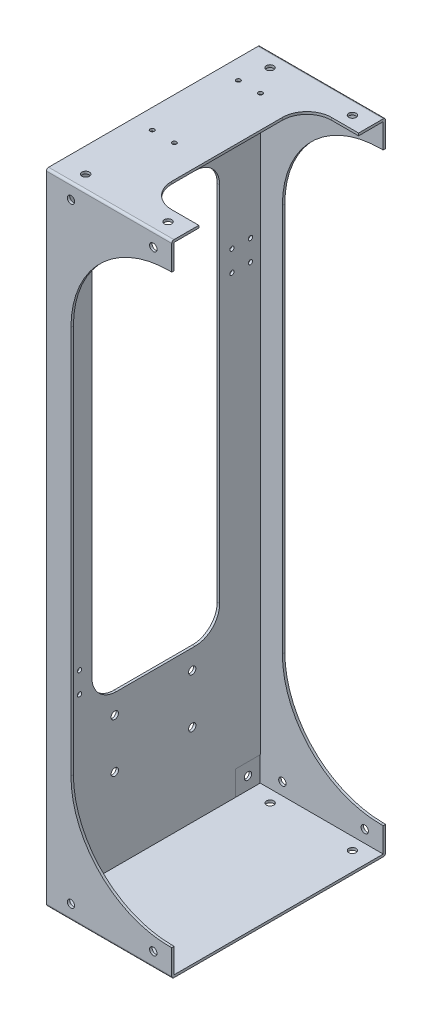
SolidWorks part; units mm, degrees
ref_plane "Front Plane" through (0, 0, 0) normal (0, 0, 1) x (1, 0, 0)
ref_plane "Top Plane" through (0, 0, 0) normal (0, 1, 0) x (1, 0, 0)
ref_plane "Right Plane" through (0, 0, 0) normal (1, 0, 0) x (0, 0, -1)
sketch "Sketch1" plane through (0, 0, 0) normal (1, 0, 0) x (0, 0, -1)
  line L0 (-87, 260) -> (87, -260) construction
  line L1 (-87, 260) -> (87, 260)
  line L2 (-87, 260) -> (-87, -260)
  line L3 (-87, -260) -> (87, -260)
  line L4 (87, 260) -> (87, -260)
  dimension "D1" = 520
  dimension "D2" = 174
extrude "Boss-Extrude1" add sketch "Sketch1" along normal blind 2
sketch "Sketch2" plane through (2, 0, 0) normal (1, 0, 0) x (0, 0, -1)
  line L8 (-85, 258) -> (-85, -258)
  line L9 (-85, -258) -> (85, -258)
  line L10 (85, -258) -> (85, 258)
  line L11 (85, 258) -> (-85, 258)
  line L12 (-85, 258) -> (-85, -258)
  line L13 (-85, -258) -> (85, -258)
  line L14 (85, -258) -> (85, 258)
  line L15 (85, 258) -> (-85, 258)
  line L16 (-87, 260) -> (-87, -260)
  line L17 (-87, -260) -> (87, -260)
  line L18 (87, -260) -> (87, 260)
  line L19 (87, 260) -> (-87, 260)
  line L20 (-87, 260) -> (-87, -260)
  line L21 (-87, -260) -> (87, -260)
  line L22 (87, -260) -> (87, 260)
  line L23 (87, 260) -> (-87, 260)
  dimension "D1" = 2
  dimension "D2" = 0
extrude "Boss-Extrude2" add sketch "Sketch2" along normal blind 100
sketch "Sketch3" plane through (0, 0, -87) normal (0, 0, 1) x (1, 0, 0)
  line L0 (102, 260) -> (0, 260) construction
  line L1 (102, 238) -> (100, 238)
  line L2 (20, 158) -> (20, -158)
  line L3 (100, -238) -> (102, -238)
  line L4 (0, 260) -> (0, -260) construction
  line L5 (102, 260) -> (102, -260) construction
  line L6 (102, -260) -> (0, -260) construction
  line L7 (102, 238) -> (102, -238)
  arc A0 (20, -158) -> (100, -238) centre (100, -158) ccw
  arc A1 (100, 238) -> (20, 158) centre (100, 158) ccw
  dimension "D3" = 80
  dimension "D2" = 20
  dimension "D11" = 22
  dimension "D12" = 22
extrude "Cut-Extrude1" cut sketch "Sketch3" along normal blind 10
sketch "Sketch4" plane through (0, 0, 87) normal (0, 0, 1) x (1, 0, 0)
  line L0 (102, 260) -> (0, 260) construction
  line L1 (102, 260) -> (102, -260) construction
  line L2 (102, -260) -> (0, -260) construction
  line L3 (0, 260) -> (0, -260) construction
  circle A0 centre (20, 248) radius 3
  circle A1 centre (87, 248) radius 3
  circle A2 centre (20, -248) radius 3
  circle A3 centre (87, -248) radius 3
  dimension "D2" = 6
  dimension "D1" = 12
  dimension "D3" = 15
  dimension "D4" = 12
  dimension "D5" = 20
extrude "Cut-Extrude2" cut sketch "Sketch4" against normal through all
sketch "Sketch5" plane through (0, 260, 0) normal (0, 1, 0) x (1, 0, 0)
  line L0 (20, 87) -> (20, 85) construction
  line L1 (87, 87) -> (87, 85) construction
  line L2 (102, -87) -> (0, -87) construction
  line L3 (102, 87) -> (0, 87) construction
  circle A0 centre (87, 75) radius 3
  circle A1 centre (20, 75) radius 3
  circle A2 centre (87, -75) radius 3
  circle A3 centre (20, -75) radius 3
  dimension "D3" = 6
  dimension "D1" = 12
  dimension "D2" = 12
extrude "Cut-Extrude3" cut sketch "Sketch5" against normal through all
sketch "Sketch7" plane through (0, 0, 87) normal (0, 0, -1) x (-1, 0, 0)
  line L0 (-102, 238) -> (-100, 238)
  line L1 (-102, -260) -> (-102, -238) construction
  line L2 (-20, 158) -> (-20, -158)
  line L3 (-102, 260) -> (0, 260) construction
  line L4 (-102, -260) -> (0, -260) construction
  line L5 (0, -260) -> (0, 260) construction
  line L6 (-102, 238) -> (-102, -238)
  line L7 (-102, -238) -> (-100, -238)
  arc A2 (-20, 158) -> (-100, 238) centre (-100, 158) ccw
  arc A3 (-20, -158) -> (-100, -238) centre (-100, -158) cw
  dimension "D5" = 80
  dimension "D1" = 22
  dimension "D2" = 22
  dimension "D3" = 20
extrude "Cut-Extrude4" cut sketch "Sketch7" along normal blind 10
sketch "Sketch8" plane through (0, 260, 0) normal (0, 1, 0) x (1, 0, 0)
  line L0 (102, 65) -> (80, 65)
  line L1 (102, 87) -> (102, -87) construction
  line L2 (60, 45) -> (60, -45)
  line L3 (80, -65) -> (102, -65)
  line L4 (102, -65) -> (102, 65)
  line L5 (102, 87) -> (0, 87) construction
  line L6 (102, -87) -> (0, -87) construction
  line L7 (0, 87) -> (0, -87) construction
  arc A0 (60, -45) -> (80, -65) centre (80, -45) ccw
  arc A1 (80, 65) -> (60, 45) centre (80, 45) ccw
  circle A2 centre (34, 53.15) radius 1.75
  circle A3 centre (16, 53.15) radius 1.75
  circle A4 centre (16, -16.85) radius 1.75
  circle A5 centre (34, -16.85) radius 1.75
  dimension "D1" = 20
  dimension "D5" = 3.5
  dimension "D2" = 22
  dimension "D3" = 22
  dimension "D4" = 60
extrude "Cut-Extrude5" cut sketch "Sketch8" against normal blind 10
fillet "Fillet1" radius 1.8 4 edges at (51, -260, 87) (51, 260, -87) (51, 260, 87) (51, -260, -87)
sketch "Sketch9" plane through (0, 0, 0) normal (-1, 0, 0) x (0, 0, 1)
  line L0 (-85.2, 260) -> (85.2, 260) construction
  line L1 (87, 258.2) -> (87, -258.2) construction
  line L2 (-87, -258.2) -> (-87, 258.2) construction
  line L3 (85.2, -260) -> (-85.2, -260) construction
  circle A0 centre (-75, 248) radius 3
  circle A1 centre (75, 248) radius 3
  circle A2 centre (75, -248) radius 3
  circle A3 centre (-75, -248) radius 3
  dimension "D5" = 6
  dimension "D1" = 12
  dimension "D2" = 12
  dimension "D3" = 12
  dimension "D4" = 12
extrude "Cut-Extrude6" cut sketch "Sketch9" against normal blind 10
sketch "Sketch10" plane through (0, 0, 0) normal (-1, 0, 0) x (0, 0, 1)
  line L0 (-87, -258.2) -> (-87, 258.2) construction
  line L1 (-32, 200) -> (32, 200)
  line L2 (-52, 180) -> (-52, -115)
  line L3 (-32, -135) -> (32, -135)
  line L4 (52, 180) -> (52, -115)
  line L5 (87, 258.2) -> (87, -258.2) construction
  line L6 (-85.2, 260) -> (85.2, 260) construction
  line L7 (85.2, -260) -> (-85.2, -260) construction
  arc A0 (-52, -115) -> (-32, -135) centre (-32, -115) ccw
  arc A1 (32, -135) -> (52, -115) centre (32, -115) ccw
  arc A2 (32, 200) -> (52, 180) centre (32, 180) cw
  arc A3 (-32, 200) -> (-52, 180) centre (-32, 180) ccw
  circle A4 centre (-29.65, -151) radius 3
  circle A5 centre (33.35, -151) radius 3
  circle A6 centre (-29.65, -191) radius 3
  circle A7 centre (33.35, -191) radius 3
  circle A8 centre (62, 233) radius 1.75
  circle A9 centre (77, 233) radius 1.75
  circle A10 centre (62, 216) radius 1.75
  circle A11 centre (77, 216) radius 1.75
  circle A12 centre (-77, 130) radius 1.75
  circle A13 centre (-62, 130) radius 1.75
  circle A14 centre (-62, 113) radius 1.75
  circle A15 centre (-77, 113) radius 1.75
  circle A16 centre (62, -105) radius 1.75
  circle A17 centre (77, -105) radius 1.75
  circle A18 centre (62, -122) radius 1.75
  circle A19 centre (77, -122) radius 1.75
  dimension "D1" = 20
  dimension "D6" = 6
  dimension "D7" = 3.5
  dimension "D2" = 35
  dimension "D3" = 35
  dimension "D4" = 60
  dimension "D5" = 125
extrude "Cut-Extrude7" cut sketch "Sketch10" against normal through all
sketch "Sketch11" plane through (2, 0, 0) normal (1, 0, 0) x (0, 0, -1)
  line L0 (-85, -238) -> (-85, -258) construction
  line L1 (-85, 258) -> (-65, 258)
  line L2 (-85, 258) -> (-85, 238)
  line L3 (-85, 238) -> (-65, 238)
  line L4 (-65, 258) -> (-65, 238)
  line L5 (85, 258) -> (65, 258)
  line L6 (85, 258) -> (85, 238)
  line L7 (85, 238) -> (65, 238)
  line L8 (65, 258) -> (65, 238)
  line L9 (65, -238) -> (85, -238)
  line L10 (65, -238) -> (65, -258)
  line L11 (65, -258) -> (85, -258)
  line L12 (85, -238) -> (85, -258)
  line L13 (-65, -238) -> (-85, -238)
  line L14 (-65, -238) -> (-65, -258)
  line L15 (-65, -258) -> (-85, -258)
  line L16 (-85, -238) -> (-85, -258)
  line L17 (-85, -258) -> (85, -258) construction
  line L18 (-85, -258) -> (85, -258) construction
  line L19 (85, -258) -> (85, 258) construction
  dimension "D1" = 20
extrude "Cut-Extrude8" cut sketch "Sketch11" against normal blind 0.01
